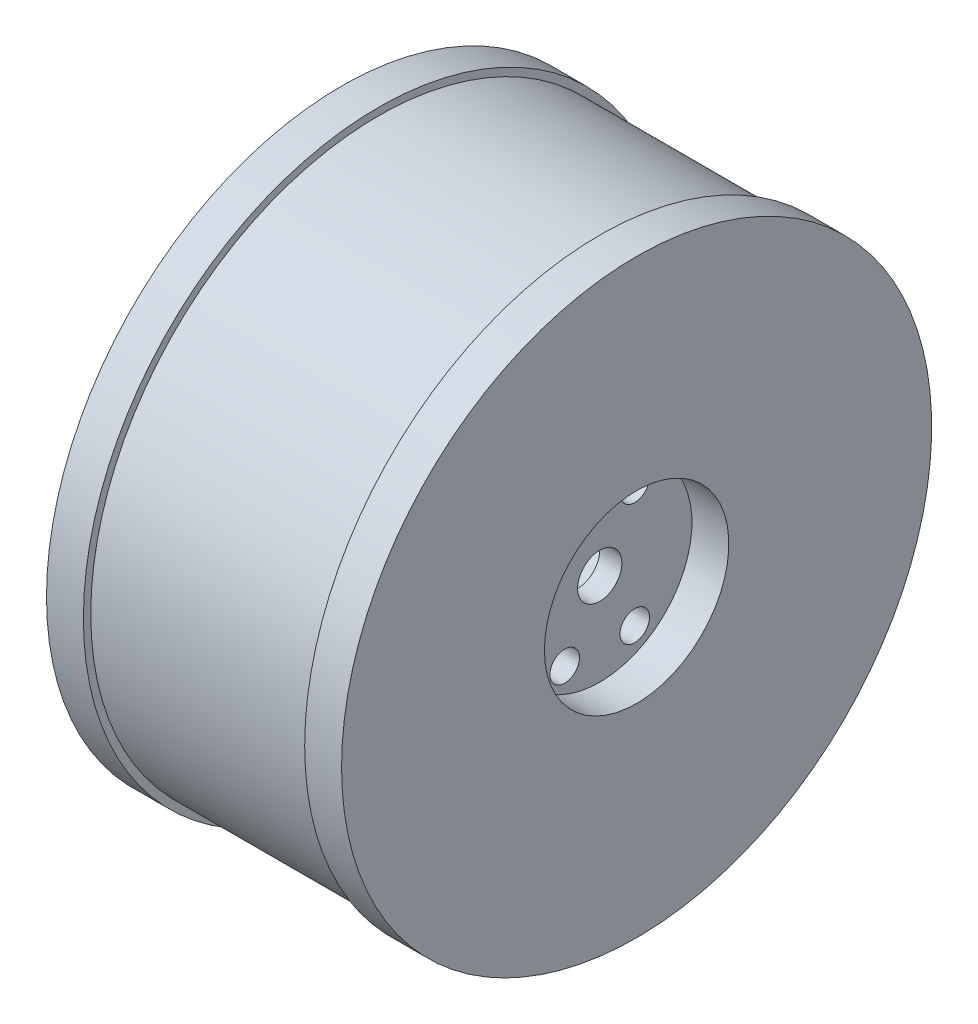
SolidWorks part; units mm, degrees
ref_plane "Plan de face" through (0, 0, 0) normal (0, 0, 1) x (1, 0, 0)
ref_plane "Plan de dessus" through (0, 0, 0) normal (0, 1, 0) x (1, 0, 0)
ref_plane "Plan de droite" through (0, 0, 0) normal (1, 0, 0) x (0, 0, -1)
sketch "Esquisse1" plane through (0, 0, 0) normal (0, 0, 1) x (1, 0, 0)
  line L0 (-49.6445, 0) -> (53.9199, 0) construction
  line L1 (0, 34) -> (0, 0)
  line L2 (0, 34) -> (-32, 34)
  line L3 (-32, 34) -> (-32, 40)
  line L4 (-32, 40) -> (-27, 40)
  line L5 (-27, 40) -> (-27, 39)
  line L6 (-27, 39) -> (3, 39)
  line L7 (3, 39) -> (3, 40)
  line L8 (3, 40) -> (8, 40)
  line L9 (8, 40) -> (8, 0)
  line L13 (0, 0) -> (8, 0)
  dimension "D2" = 5
  dimension "D3" = 5
  dimension "D4" = 40
  dimension "D5" = 1
  dimension "D6" = 8
  dimension "D10" = 6
  dimension "D11" = 1
  dimension "D12" = 30
revolve "Révolution1" add sketch "Esquisse1" angle 360 about L0
sketch "Esquisse2" plane through (0, 0, 0) normal (0, 0, 1) x (1, 0, 0)
  line L3 (0, 0) -> (8, 0) construction
  line L11 (8, -40) -> (8, 40) construction
  line L12 (8, 0) -> (8, 12.5)
  line L13 (8, 12.5) -> (3, 12.5)
  line L14 (3, 12.5) -> (3, 0)
  line L15 (3, 0) -> (8, 0)
  dimension "D1" = 25
  dimension "D2" = 5
revolve "Enlèvement de matière-Révolution1" cut sketch "Esquisse2" angle 360 about L3
sketch "Esquisse3" plane through (3, 0, 0) normal (1, 0, 0) x (0, 0, -1)
  line L0 (0, 12.5) -> (0, 0) construction
  line L1 (0, 0) -> (12.5, 0) construction
  line L2 (4.75, 8.2272) -> (0, 0) construction
  circle A0 centre (4.75, 8.2272) radius 2
  circle A2 centre (0, 0) radius 12.5 construction
  circle A3 centre (0, 0) radius 12.5 construction
  circle A4 centre (-4.75, 8.2272) radius 2
  circle A5 centre (4.75, -8.2272) radius 2
  circle A6 centre (-4.75, -8.2272) radius 2
  dimension "D1" = 4
  dimension "D2" = 9.5
  dimension "D3" = 30
extrude "Enlèv. mat.-Extru.1" cut sketch "Esquisse3" against normal through all
sketch "Esquisse4" plane through (3, 0, 0) normal (1, 0, 0) x (0, 0, -1)
  circle A0 centre (0, 0) radius 3
  dimension "D1" = 6
extrude "Enlèv. mat.-Extru.2" cut sketch "Esquisse4" against normal through all
